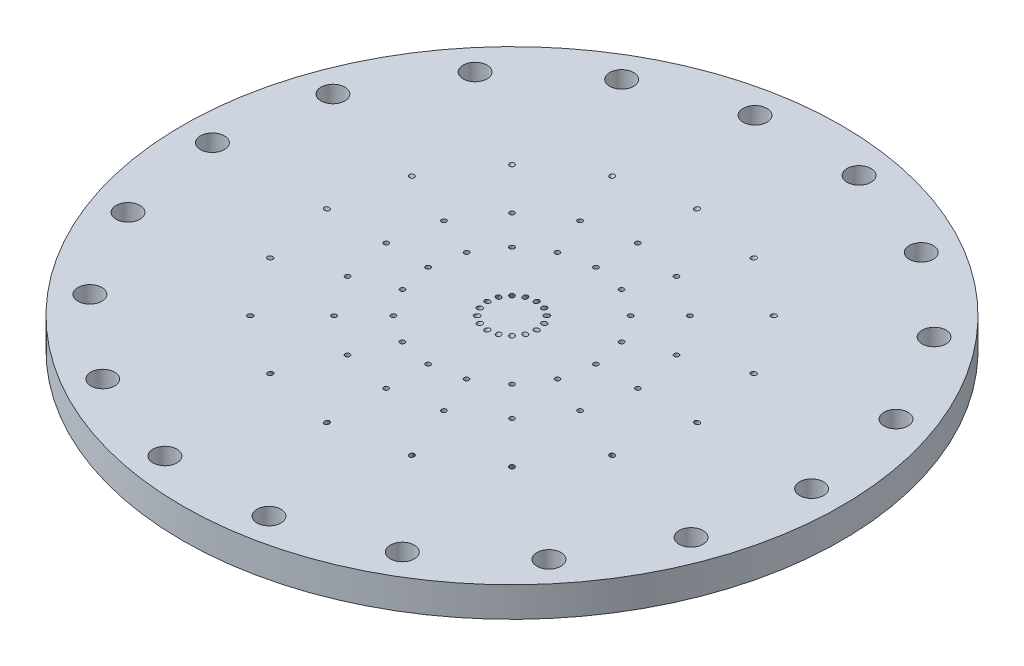
SolidWorks part; units mm, degrees
material "6061-T6 (SS)"
ref_plane "Front Plane" through (0, 0, 0) normal (0, 0, 1) x (1, 0, 0)
ref_plane "Top Plane" through (0, 0, 0) normal (0, 1, 0) x (1, 0, 0)
ref_plane "Right Plane" through (0, 0, 0) normal (1, 0, 0) x (0, 0, -1)
sketch "Sketch1" plane through (0, 0, 0) normal (0, 1, 0) x (1, 0, 0)
  circle A0 centre (0, 0) radius 69.85
  dimension "D1" = 139.7
extrude "Boss-Extrude1" add sketch "Sketch1" along normal blind 6.35
sketch "Sketch2" plane through (0, 0, 0) normal (0, -1, 0) x (1, 0, 0)
  circle A0 centre (0, 0) radius 69.85
  circle A1 centre (0, 0) radius 69.85 construction
extrude "Boss-Extrude2" add sketch "Sketch2" along normal blind 6.35
sketch "Sketch3" plane through (0, -6.35, 0) normal (0, -1, 0) x (1, 0, 0)
  circle A0 centre (0, 0) radius 17.78
  circle A1 centre (0, 0) radius 8.89
  circle A2 centre (0, 0) radius 35.56
  circle A3 centre (0, 0) radius 26.67
  dimension "D1" = 35.56
  dimension "D2" = 17.78
  dimension "D3" = 53.34
  dimension "D4" = 71.12
sketch "Sketch4" plane through (0, 6.35, 0) normal (0, 1, 0) x (1, 0, 0)
  circle A0 centre (0, 0) radius 6.35
  dimension "D1" = 12.7
extrude "Cut-Extrude1" cut sketch "Sketch4" against normal blind 6.35
sketch "Sketch5" plane through (0, 6.35, 0) normal (0, 1, 0) x (1, 0, 0)
  circle A0 centre (0, 0) radius 12.7
  circle A1 centre (0, 0) radius 26.1937
  dimension "D1" = 25.4
  dimension "D2" = 52.3875
extrude "Cut-Extrude2" cut sketch "Sketch5" against normal blind 6.35
sketch "Sketch6" plane through (0, 6.35, 0) normal (0, 1, 0) x (1, 0, 0)
  circle A0 centre (0, 0) radius 31.75
  circle A1 centre (0, 0) radius 36.83
  dimension "D1" = 73.66
  dimension "D2" = 63.5
extrude "Cut-Extrude3" cut sketch "Sketch6" against normal blind 6.35
sketch "Sketch7" plane through (0, 0, 0) normal (0, 0, 1) x (1, 0, 0)
  line L0 (-39.9594, 1.27) -> (-31.1606, -13.97)
  line L2 (-35.56, -6.35) -> (-38.0769, -6.35) construction
  line L3 (-35.56, -6.35) -> (35.56, -6.35) construction
  line L4 (-31.1606, -13.97) -> (-36.6965, -17.1662) construction
  point P5 (-35.56, -6.35)
  dimension "D1" = 60
  dimension "D2" = 7.62
ref_plane "Plane1" through (-1.741, 3.0154, 0) normal (-0.5, 0.866, 0) x (-0.866, -0.5, 0)
sketch "Sketch8" plane through (-1.741, 3.0154, 0) normal (-0.5, 0.866, 0) x (-0.866, -0.5, 0)
  line L0 (33.9709, 0) -> (40.3632, 0) construction
  circle A0 centre (33.9709, 0) radius 0.508
  dimension "D1" = 1.016
extrude "Cut-Extrude4" cut sketch "Sketch8" along normal up to next
sketch "Sketch9" plane through (0, -6.35, 0) normal (0, -1, 0) x (1, 0, 0)
  line L0 (0, 0) -> (-35.56, 0) construction
  circle A0 centre (-26.67, 0) radius 0.508
  circle A1 centre (-17.78, 0) radius 0.508
  circle A5 centre (0, 0) radius 17.78 construction
  circle A6 centre (0, 0) radius 26.67 construction
  dimension "D1" = 1.016
extrude "Cut-Extrude5" cut sketch "Sketch9" against normal up to next (12.7 mm away)
sketch "Sketch10" plane through (0, 0, 0) normal (0, 0, 1) x (1, 0, 0)
  line L0 (-14.5398, -16.1358) -> (-3.2402, 3.4358)
  line L2 (-8.89, -6.35) -> (-21.7665, -6.35) construction
  line L5 (-14.5398, -16.1358) -> (-3.6009, -22.4514) construction
  point P5 (-8.89, -6.35)
  dimension "D1" = 60
ref_plane "Plane2" through (-10.622, -18.3978, 0) normal (0.5, 0.866, 0) x (0.866, -0.5, 0)
sketch "Sketch11" plane through (-10.622, -18.3978, 0) normal (0.5, 0.866, 0) x (0.866, -0.5, 0)
  circle A0 centre (-4.524, 0) radius 0.508
  dimension "D1" = 1.016
extrude "Cut-Extrude6" cut sketch "Sketch11" along normal up to next
pattern_circular "CirPattern1" count 16 over 360 about axis through (0, 0, 0) along (0, 1, 0) of "Cut-Extrude6", "Cut-Extrude4", "Cut-Extrude5"
sketch "Sketch12" plane through (0, 6.35, 0) normal (0, 1, 0) x (1, 0, 0)
  circle A0 centre (0, 0) radius 63.5 construction
  circle A1 centre (63.5, 0) radius 2.54
  dimension "D1" = 127
  dimension "D2" = 5.08
extrude "Cut-Extrude7" cut sketch "Sketch12" against normal through all
pattern_circular "CirPattern2" count 18 over 360 about axis through (0, 0, 0) along (0, 1, 0) of "Cut-Extrude7"
sketch "Sketch13" plane through (0, 6.35, 0) normal (0, 1, 0) x (1, 0, 0)
  circle A0 centre (0, 0) radius 7.7216
  circle A1 centre (0, 0) radius 10.3632
  dimension "D1" = 2.6416
  dimension "D2" = 20.7264
extrude "Cut-Extrude8" cut sketch "Sketch13" against normal blind 1.3208
sketch "Sketch14" plane through (0, 6.35, 0) normal (0, 1, 0) x (1, 0, 0)
  circle A0 centre (0, 0) radius 27.5717
  circle A1 centre (0, 0) radius 30.2133
  dimension "D1" = 2.6416
  dimension "D2" = 60.4266
extrude "Cut-Extrude9" cut sketch "Sketch14" against normal blind 1.3208
sketch "Sketch16" plane through (0, 6.35, 0) normal (0, 1, 0) x (1, 0, 0)
  circle A0 centre (0, 0) radius 43.4467
  circle A1 centre (0, 0) radius 46.0883
  dimension "D1" = 2.6416
  dimension "D2" = 92.1766
extrude "Cut-Extrude10" cut sketch "Sketch16" against normal blind 1.3208
sketch "Sketch20" plane through (0, 6.35, 0) normal (0, 1, 0) x (1, 0, 0)
  circle A0 centre (0, 0) radius 69.85
extrude "Cut-Extrude11" cut sketch "Sketch20" against normal up to surface (6.35 mm away) up to face at (16.4266, 0, 7.3121)
